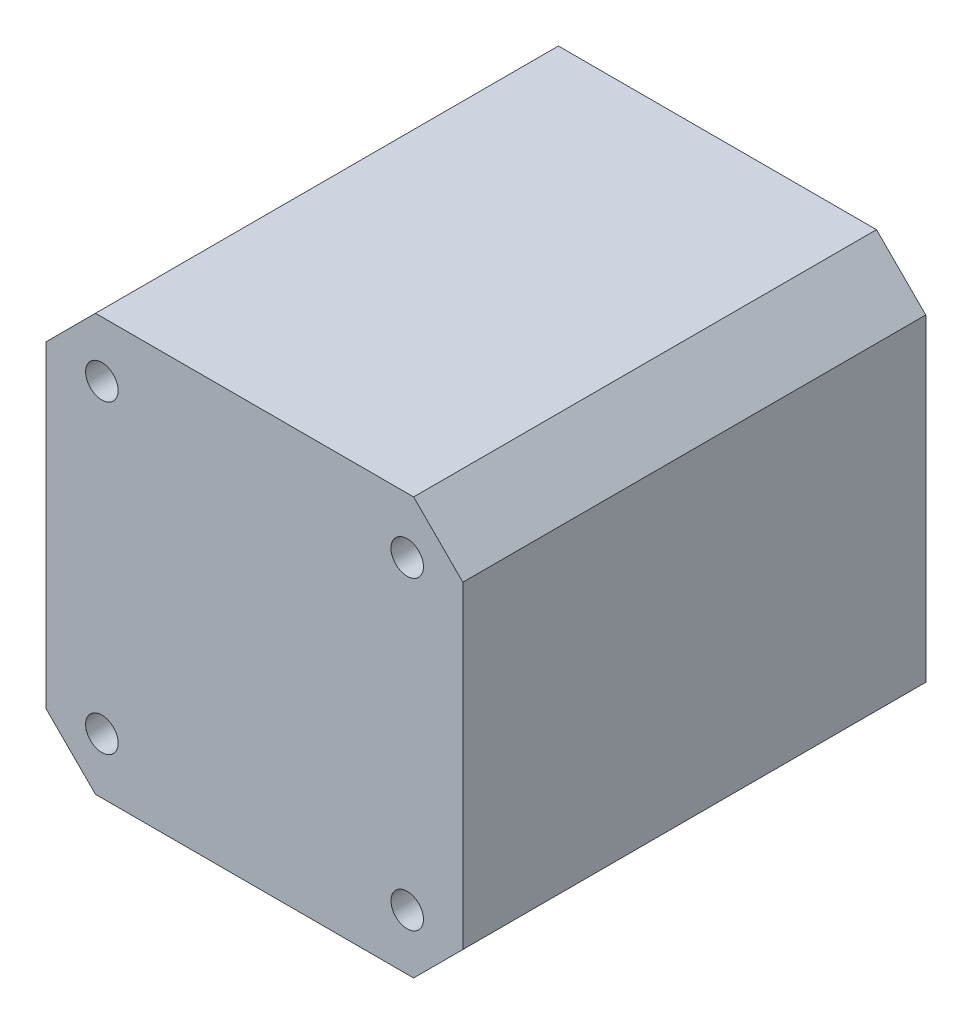
SolidWorks part; units mm, degrees
ref_plane "前视基准面" through (0, 0, 0) normal (0, 0, 1) x (1, 0, 0)
ref_plane "上视基准面" through (0, 0, 0) normal (0, 1, 0) x (1, 0, 0)
ref_plane "右视基准面" through (0, 0, 0) normal (1, 0, 0) x (0, 0, -1)
sketch "草图1" plane through (0, 0, 0) normal (0, 0, 1) x (1, 0, 0)
  line L0 (-21.15, 16.15) -> (-16.15, 21.15)
  line L1 (-16.15, 21.15) -> (16.15, 21.15)
  line L2 (-21.15, 16.15) -> (-21.15, -16.15)
  line L3 (-16.15, -21.15) -> (16.15, -21.15)
  line L4 (21.15, 16.15) -> (21.15, -16.15)
  line L5 (-21.15, 21.15) -> (21.15, -21.15) construction
  line L6 (-21.15, -21.15) -> (21.15, 21.15) construction
  line L7 (16.15, 21.15) -> (21.15, 16.15)
  line L8 (16.15, -21.15) -> (21.15, -16.15)
  line L9 (-21.15, -16.15) -> (-16.15, -21.15)
  line L10 (0, 0) -> (0, 11) construction
  line L11 (11, 0) -> (0, 0) construction
  circle A1 centre (15.5, 15.5) radius 1.65
  circle A2 centre (-15.5, 15.5) radius 1.65
  circle A3 centre (15.5, -15.5) radius 1.65
  circle A4 centre (-15.5, -15.5) radius 1.65
  point P0 (0, 0)
  dimension "D4" = 3.3
  dimension "D1" = 42.3
  dimension "D2" = 42.3
  dimension "D5" = 31
extrude "凸台-拉伸1" add sketch "草图1" along normal blind 47
sketch "草图3" plane through (0, 0, 0) normal (0, 0, -1) x (-1, 0, 0)
  circle A0 centre (0, 0) radius 11
  dimension "D1" = 22
extrude "凸台-拉伸2" add sketch "草图3" along normal blind 2
sketch "草图4" plane through (0, 0, -2) normal (0, 0, -1) x (-1, 0, 0)
  line L0 (-1.5, 2) -> (1.5, 2)
  arc A0 (-1.5, 2) -> (1.5, 2) centre (0, 0) ccw
  dimension "D1" = 5
  dimension "D2" = 2
extrude "凸台-拉伸3" add sketch "草图4" along normal blind 22
sketch "草图5" plane through (0, 0, -24) normal (0, 0, -1) x (-1, 0, 0)
  line L1 (1.5, 2) -> (-1.5, 2)
  line L2 (1.5, 2) -> (-1.5, 2)
  arc A1 (-1.5, 2) -> (1.5, 2) centre (0, 0) ccw
  arc A2 (-1.5, 2) -> (1.5, 2) centre (0, 0) ccw
  dimension "D1" = 0
extrude "切除-拉伸1" cut sketch "草图5" against normal blind 10
